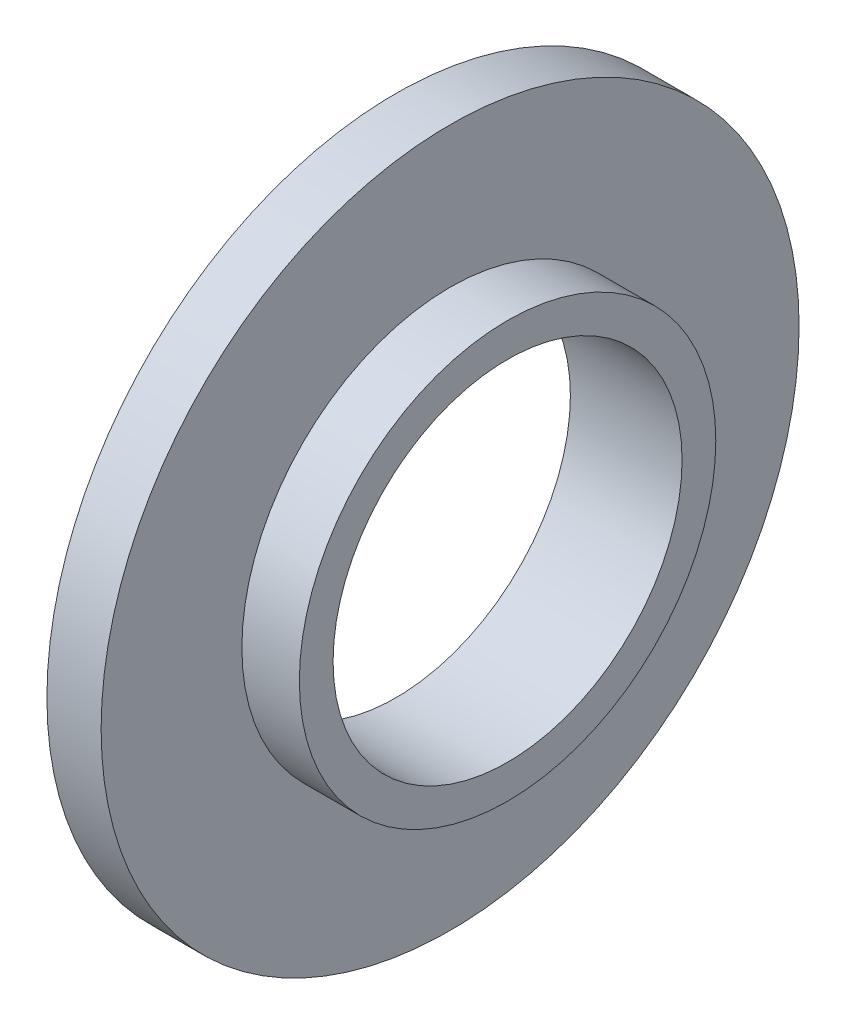
SolidWorks part; units mm, degrees
ref_plane "前视基准面" through (0, 0, 0) normal (0, 0, 1) x (1, 0, 0)
ref_plane "上视基准面" through (0, 0, 0) normal (0, 1, 0) x (1, 0, 0)
ref_plane "右视基准面" through (0, 0, 0) normal (1, 0, 0) x (0, 0, -1)
sketch "草图1" plane through (0, 0, 0) normal (1, 0, 0) x (0, 0, -1)
  circle A0 centre (0, 0) radius 30
extrude "凸台-拉伸1" add sketch "草图1" along normal blind 4.66
sketch "草图2" plane through (4.66, 0, 0) normal (1, 0, 0) x (0, 0, -1)
  circle A0 centre (0, 0) radius 17.9
extrude "凸台-拉伸2" add sketch "草图2" along normal blind 4.94
sketch "草图3" plane through (9.6, 0, 0) normal (1, 0, 0) x (0, 0, -1)
  circle A0 centre (0, 0) radius 15
extrude "切除-拉伸1" cut sketch "草图3" against normal through all
